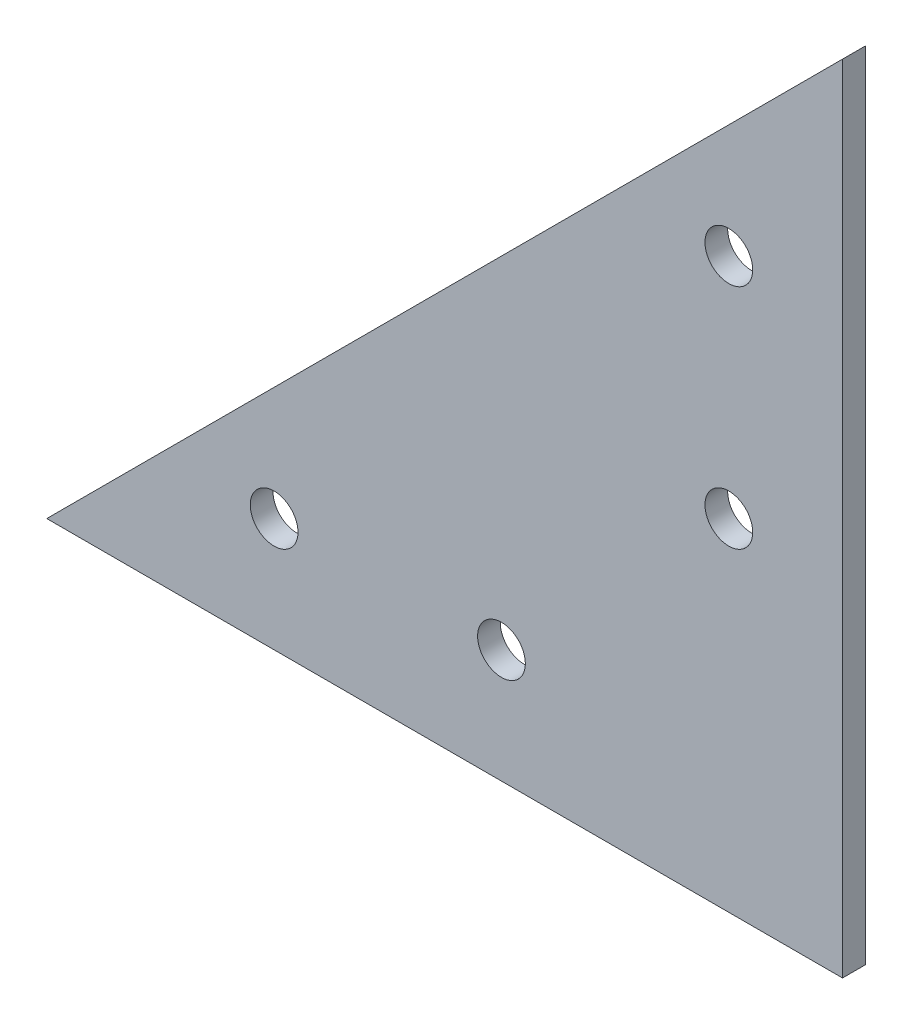
SolidWorks part; units mm, degrees
ref_plane "正面" through (0, 0, 0) normal (0, 0, 1) x (1, 0, 0)
ref_plane "平面" through (0, 0, 0) normal (0, 1, 0) x (1, 0, 0)
ref_plane "右側面" through (0, 0, 0) normal (1, 0, 0) x (0, 0, -1)
sketch "ｽｹｯﾁ1" plane through (0, 0, 0) normal (0, 0, 1) x (1, 0, 0)
  line L0 (0, 0) -> (0, 70)
  line L1 (0, 70) -> (-70, 0)
  line L2 (-70, 0) -> (0, 0)
  line L3 (-10, 10) -> (-10, 50)
  line L4 (0, 0) -> (-10, 0)
  line L5 (0, 0) -> (0, 10)
  line L6 (0, 10) -> (-10, 10)
  line L7 (-10, 0) -> (-10, 10)
  line L8 (-10, 10) -> (-50, 10)
  line L9 (-10, 10) -> (-10, 30)
  line L10 (-10, 10) -> (-30, 10)
  circle A0 centre (-10, 50) radius 2.1
  circle A1 centre (-10, 10) radius 2.1
  circle A2 centre (-50, 10) radius 2.1
  circle A3 centre (-10, 30) radius 2.1
  circle A4 centre (-30, 10) radius 2.1
  dimension "D7" = 4.2
  dimension "D8" = 4.2
  dimension "D9" = 4.2
  dimension "D10" = 4.2
  dimension "D11" = 4.2
  dimension "D1" = 10
  dimension "D2" = 10
  dimension "D3" = 40
  dimension "D4" = 40
  dimension "D5" = 70
  dimension "D6" = 70
extrude "ﾎﾞｽ - 押し出し1" add sketch "ｽｹｯﾁ1" along normal blind 2
